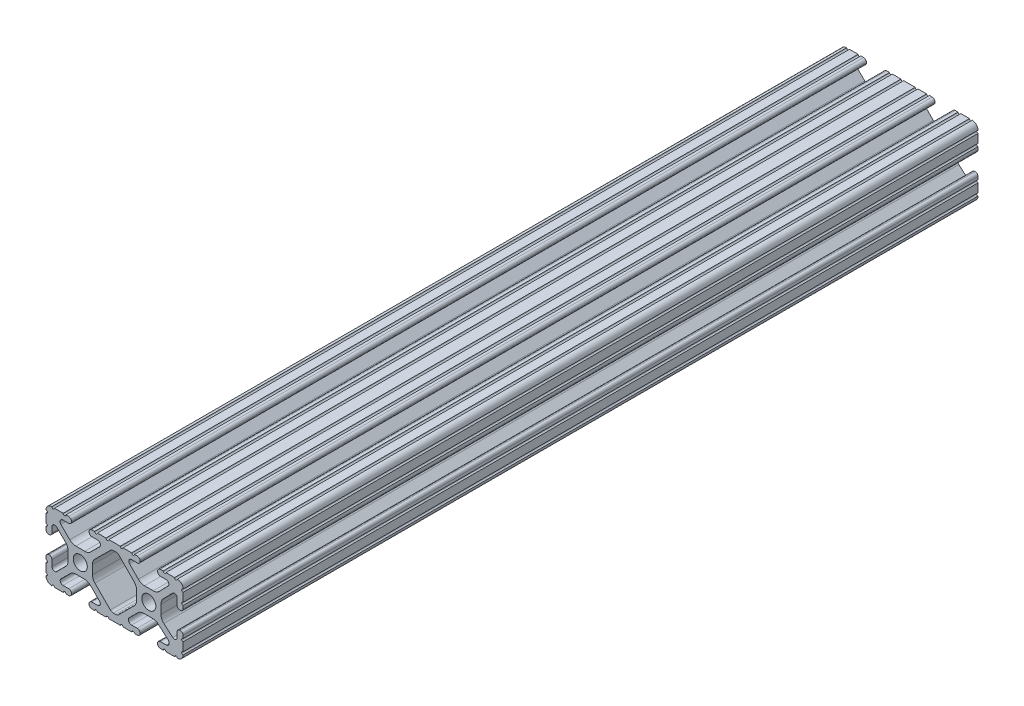
SolidWorks part; units mm, degrees
material "6061 Alloy"
ref_plane "Front Plane" through (0, 0, 0) normal (0, 0, 1) x (1, 0, 0)
ref_plane "Top Plane" through (0, 0, 0) normal (0, 1, 0) x (1, 0, 0)
ref_plane "Right Plane" through (0, 0, 0) normal (1, 0, 0) x (0, 0, -1)
sketch "Sketch1" plane through (0, 0, 0) normal (0, 0, 1) x (1, 0, 0)
  line L0 (-32.9707, 0) -> (32.2708, 0) construction
  line L1 (0, 12.7) -> (0, 0) construction
  line L2 (-12.7, 14.992) -> (-12.7, -12.6999) construction
  line L3 (12.7, 13.9801) -> (12.7, -13.3809) construction
  line L4 (-7.2595, -3.8694) -> (-1.5457, -9.5728)
  line L5 (1.5457, -9.5728) -> (7.2595, -3.8694)
  line L7 (-0.3952, 10.033) -> (0.5515, 10.033)
  line L9 (0.4332, -10.033) -> (-0.4332, -10.033)
  line L12 (8.1915, -1.6223) -> (8.1915, 1.6223)
  line L13 (7.2829, 3.8459) -> (1.6756, 9.5611)
  line L14 (-1.504, 9.5765) -> (-7.252, 3.8768)
  line L15 (-8.1915, 1.6223) -> (-8.1915, -1.6223)
  line L16 (22.2504, 12.7) -> (19.0331, 12.7)
  line L17 (18.0171, 12.7) -> (16.9875, 12.7)
  line L18 (15.9385, 11.651) -> (15.9385, 11.5392)
  line L19 (16.9875, 10.4902) -> (19.1164, 10.4902)
  line L20 (19.8441, 8.7652) -> (16.619, 5.4551)
  line L21 (14.3449, 4.4958) -> (11.0833, 4.4958)
  line L22 (8.817, 5.4472) -> (5.5642, 8.7627)
  line L23 (6.2894, 10.4902) -> (8.4125, 10.4902)
  line L24 (9.4615, 11.5392) -> (9.4615, 11.651)
  line L25 (8.4125, 12.7) -> (7.3829, 12.7)
  line L26 (6.3669, 12.7) -> (3.1496, 12.7)
  line L27 (2.1336, 12.7) -> (-2.1336, 12.7)
  line L28 (-3.1496, 12.7) -> (-6.3669, 12.7)
  line L29 (-7.3829, 12.7) -> (-8.4125, 12.7)
  line L30 (-9.4615, 11.651) -> (-9.4615, 11.5392)
  line L31 (-8.4125, 10.4902) -> (-6.2836, 10.4902)
  line L32 (-5.5326, 8.6661) -> (-8.81, 5.4163)
  line L33 (-11.0455, 4.4958) -> (-14.3545, 4.4958)
  line L34 (-16.59, 5.4163) -> (-19.8674, 8.6661)
  line L35 (-19.1164, 10.4902) -> (-16.9875, 10.4902)
  line L36 (-15.9385, 11.5392) -> (-15.9385, 11.651)
  line L37 (-16.9875, 12.7) -> (-18.0171, 12.7)
  line L38 (-19.0331, 12.7) -> (-22.2504, 12.7)
  line L39 (-25.4, 9.5504) -> (-25.4, 6.3331)
  line L40 (-25.4, 5.3171) -> (-25.4, 4.2375)
  line L41 (-24.401, 3.2385) -> (-24.2392, 3.2385)
  line L42 (-23.1902, 4.2875) -> (-23.1902, 6.3347)
  line L43 (-21.434, 7.0665) -> (-18.148, 3.8082)
  line L44 (-17.2085, 1.5536) -> (-17.2085, -1.6952)
  line L45 (-18.1405, -3.9423) -> (-21.4316, -7.2274)
  line L46 (-23.1902, -6.498) -> (-23.1902, -4.2875)
  line L47 (-24.2392, -3.2385) -> (-24.351, -3.2385)
  line L48 (-25.4, -4.2875) -> (-25.4, -5.3171)
  line L49 (-25.4, -6.3331) -> (-25.4, -9.5504)
  line L50 (-22.2504, -12.7) -> (-19.0331, -12.7)
  line L51 (-18.0171, -12.7) -> (-16.9875, -12.7)
  line L52 (-15.9384, -11.651) -> (-15.9384, -11.5392)
  line L53 (-16.9875, -10.4902) -> (-19.1164, -10.4902)
  line L54 (-19.8341, -8.7551) -> (-16.4966, -5.4237)
  line L55 (-14.2536, -4.4958) -> (-11.1464, -4.4958)
  line L56 (-8.9034, -5.4237) -> (-5.5659, -8.7551)
  line L57 (-6.2836, -10.4902) -> (-8.4125, -10.4902)
  line L58 (-9.4616, -11.5392) -> (-9.4616, -11.651)
  line L59 (-8.4125, -12.7) -> (-7.3829, -12.7)
  line L60 (-6.3669, -12.7) -> (-3.1496, -12.7)
  line L61 (-2.1336, -12.7) -> (2.1336, -12.7)
  line L62 (3.1496, -12.7) -> (6.3669, -12.7)
  line L63 (7.3829, -12.7) -> (8.4125, -12.7)
  line L64 (9.4616, -11.651) -> (9.4616, -11.5392)
  line L65 (8.4125, -10.4902) -> (6.2894, -10.4902)
  line L66 (5.4807, -8.5353) -> (8.5979, -5.4237)
  line L67 (10.8409, -4.4958) -> (14.1026, -4.4958)
  line L68 (16.1879, -5.2766) -> (19.8682, -8.4822)
  line L69 (19.1164, -10.4902) -> (16.9875, -10.4902)
  line L70 (15.9384, -11.5392) -> (15.9384, -11.651)
  line L71 (16.9875, -12.7) -> (18.0171, -12.7)
  line L72 (19.0331, -12.7) -> (22.2504, -12.7)
  line L73 (25.4, -9.5504) -> (25.4, -6.3331)
  line L74 (25.4, -5.3171) -> (25.4, -4.2375)
  line L75 (24.401, -3.2385) -> (24.1892, -3.2385)
  line L76 (23.1902, -4.2375) -> (23.1902, -6.1559)
  line L77 (21.584, -6.8869) -> (18.2982, -4.025)
  line L78 (17.2085, -1.6308) -> (17.2085, 1.6308)
  line L79 (18.1094, 3.8465) -> (21.5263, 7.3534)
  line L80 (23.1902, 6.6769) -> (23.1902, 4.2375)
  line L81 (24.1892, 3.2385) -> (24.401, 3.2385)
  line L82 (25.4, 4.2375) -> (25.4, 5.3171)
  line L83 (25.4, 6.3332) -> (25.4, 9.5504)
  circle A0 centre (-12.7, 0) radius 2.6035
  circle A1 centre (12.7, 0) radius 2.6035
  arc A2 (-0.3952, 10.033) -> (-1.504, 9.5765) centre (-0.3952, 8.4582) ccw
  arc A3 (0.5515, 10.033) -> (1.6756, 9.5611) centre (0.5515, 8.4582) cw
  arc A4 (-8.1915, -1.6223) -> (-7.2595, -3.8694) centre (-5.0165, -1.6223) ccw
  arc A5 (-0.4332, -10.033) -> (-1.5457, -9.5728) centre (-0.4332, -8.4582) cw
  arc A6 (7.2595, -3.8694) -> (8.1915, -1.6223) centre (5.0165, -1.6223) ccw
  arc A7 (8.1915, 1.6223) -> (7.2829, 3.8459) centre (5.0165, 1.6223) ccw
  arc A8 (0.4332, -10.033) -> (1.5457, -9.5728) centre (0.4332, -8.4582) ccw
  arc A9 (-7.252, 3.8768) -> (-8.1915, 1.6223) centre (-5.0165, 1.6223) ccw
  arc A16 (25.3998, 10.5664) -> (23.2664, 12.6998) centre (23.2918, 10.5918) ccw
  arc A17 (22.2504, 12.7) -> (23.2664, 12.6998) centre (22.7584, 12.7) ccw
  arc A18 (18.0171, 12.7) -> (19.0331, 12.7) centre (18.5251, 12.7) ccw
  arc A19 (16.9875, 12.7) -> (15.9385, 11.651) centre (16.9875, 11.651) ccw
  arc A20 (15.9385, 11.5392) -> (16.9875, 10.4902) centre (16.9875, 11.5392) ccw
  arc A21 (19.8441, 8.7652) -> (19.1164, 10.4902) centre (19.1164, 9.4742) ccw
  arc A22 (14.3449, 4.4958) -> (16.619, 5.4551) centre (14.3449, 7.6708) ccw
  arc A23 (8.817, 5.4472) -> (11.0833, 4.4958) centre (11.0833, 7.6708) ccw
  arc A24 (6.2894, 10.4902) -> (5.5642, 8.7627) centre (6.2894, 9.4742) ccw
  arc A25 (8.4125, 10.4902) -> (9.4615, 11.5392) centre (8.4125, 11.5392) ccw
  arc A26 (9.4615, 11.651) -> (8.4125, 12.7) centre (8.4125, 11.651) ccw
  arc A27 (6.3669, 12.7) -> (7.3829, 12.7) centre (6.8749, 12.7) ccw
  arc A28 (2.1336, 12.7) -> (3.1496, 12.7) centre (2.6416, 12.7) ccw
  arc A29 (-3.1496, 12.7) -> (-2.1336, 12.7) centre (-2.6416, 12.7) ccw
  arc A30 (-7.3829, 12.7) -> (-6.3669, 12.7) centre (-6.8749, 12.7) ccw
  arc A31 (-8.4125, 12.7) -> (-9.4615, 11.651) centre (-8.4125, 11.651) ccw
  arc A32 (-9.4615, 11.5392) -> (-8.4125, 10.4902) centre (-8.4125, 11.5392) ccw
  arc A33 (-5.5326, 8.6661) -> (-6.2836, 10.4902) centre (-6.2836, 9.4235) ccw
  arc A34 (-11.0455, 4.4958) -> (-8.81, 5.4163) centre (-11.0455, 7.6708) ccw
  arc A35 (-16.59, 5.4163) -> (-14.3545, 4.4958) centre (-14.3545, 7.6708) ccw
  arc A36 (-19.1164, 10.4902) -> (-19.8674, 8.6661) centre (-19.1164, 9.4235) ccw
  arc A37 (-16.9875, 10.4902) -> (-15.9385, 11.5392) centre (-16.9875, 11.5392) ccw
  arc A38 (-15.9385, 11.651) -> (-16.9875, 12.7) centre (-16.9875, 11.651) ccw
  arc A39 (-19.0331, 12.7) -> (-18.0171, 12.7) centre (-18.5251, 12.7) ccw
  arc A40 (-23.2664, 12.6998) -> (-22.2504, 12.7) centre (-22.7584, 12.7) ccw
  arc A41 (-23.2664, 12.6998) -> (-25.3998, 10.5664) centre (-23.2918, 10.5918) ccw
  arc A42 (-25.4, 9.5504) -> (-25.3998, 10.5664) centre (-25.4, 10.0584) ccw
  arc A43 (-25.4, 5.3171) -> (-25.4, 6.3331) centre (-25.4, 5.8251) ccw
  arc A44 (-25.4, 4.2375) -> (-24.401, 3.2385) centre (-24.401, 4.2375) ccw
  arc A45 (-24.2392, 3.2385) -> (-23.1902, 4.2875) centre (-24.2392, 4.2875) ccw
  arc A46 (-21.434, 7.0665) -> (-23.1902, 6.3347) centre (-22.1596, 6.3347) ccw
  arc A47 (-17.2085, 1.5536) -> (-18.148, 3.8082) centre (-20.3835, 1.5536) ccw
  arc A48 (-18.1405, -3.9423) -> (-17.2085, -1.6952) centre (-20.3835, -1.6952) ccw
  arc A49 (-23.1902, -6.498) -> (-21.4316, -7.2274) centre (-22.1596, -6.498) ccw
  arc A50 (-23.1902, -4.2875) -> (-24.2392, -3.2385) centre (-24.2392, -4.2875) ccw
  arc A51 (-24.351, -3.2385) -> (-25.4, -4.2875) centre (-24.351, -4.2875) ccw
  arc A52 (-25.4, -6.3331) -> (-25.4, -5.3171) centre (-25.4, -5.8251) ccw
  arc A53 (-25.3998, -10.5664) -> (-25.4, -9.5504) centre (-25.4, -10.0584) ccw
  arc A54 (-25.3998, -10.5664) -> (-23.2664, -12.6998) centre (-23.2918, -10.5918) ccw
  arc A55 (-22.2504, -12.7) -> (-23.2664, -12.6998) centre (-22.7584, -12.7) ccw
  arc A56 (-18.0171, -12.7) -> (-19.0331, -12.7) centre (-18.5251, -12.7) ccw
  arc A57 (-16.9875, -12.7) -> (-15.9384, -11.651) centre (-16.9875, -11.651) ccw
  arc A58 (-15.9384, -11.5392) -> (-16.9875, -10.4902) centre (-16.9875, -11.5392) ccw
  arc A59 (-19.8341, -8.7551) -> (-19.1164, -10.4902) centre (-19.1164, -9.4742) ccw
  arc A60 (-14.2536, -4.4958) -> (-16.4966, -5.4237) centre (-14.2536, -7.6708) ccw
  arc A61 (-8.9034, -5.4237) -> (-11.1464, -4.4958) centre (-11.1464, -7.6708) ccw
  arc A62 (-6.2836, -10.4902) -> (-5.5659, -8.7551) centre (-6.2836, -9.4742) ccw
  arc A63 (-8.4125, -10.4902) -> (-9.4616, -11.5392) centre (-8.4125, -11.5392) ccw
  arc A64 (-9.4616, -11.651) -> (-8.4125, -12.7) centre (-8.4125, -11.651) ccw
  arc A65 (-6.3669, -12.7) -> (-7.3829, -12.7) centre (-6.8749, -12.7) ccw
  arc A66 (-2.1336, -12.7) -> (-3.1496, -12.7) centre (-2.6416, -12.7) ccw
  arc A67 (3.1496, -12.7) -> (2.1336, -12.7) centre (2.6416, -12.7) ccw
  arc A68 (7.3829, -12.7) -> (6.3669, -12.7) centre (6.8749, -12.7) ccw
  arc A69 (8.4125, -12.7) -> (9.4616, -11.651) centre (8.4125, -11.651) ccw
  arc A70 (9.4616, -11.5392) -> (8.4125, -10.4902) centre (8.4125, -11.5392) ccw
  arc A71 (5.4807, -8.5353) -> (6.2894, -10.4902) centre (6.2894, -9.3455) ccw
  arc A72 (10.8409, -4.4958) -> (8.5979, -5.4237) centre (10.8409, -7.6708) ccw
  arc A73 (16.1879, -5.2766) -> (14.1026, -4.4958) centre (14.1026, -7.6708) ccw
  arc A74 (19.1164, -10.4902) -> (19.8682, -8.4822) centre (19.1164, -9.3455) ccw
  arc A75 (16.9875, -10.4902) -> (15.9384, -11.5392) centre (16.9875, -11.5392) ccw
  arc A76 (15.9384, -11.651) -> (16.9875, -12.7) centre (16.9875, -11.651) ccw
  arc A77 (19.0331, -12.7) -> (18.0171, -12.7) centre (18.5251, -12.7) ccw
  arc A78 (23.2664, -12.6998) -> (22.2504, -12.7) centre (22.7584, -12.7) ccw
  arc A79 (23.2664, -12.6998) -> (25.3998, -10.5664) centre (23.2918, -10.5918) ccw
  arc A80 (25.4, -9.5504) -> (25.3998, -10.5664) centre (25.4, -10.0584) ccw
  arc A81 (25.4, -5.3171) -> (25.4, -6.3331) centre (25.4, -5.8251) ccw
  arc A82 (25.4, -4.2375) -> (24.401, -3.2385) centre (24.401, -4.2375) ccw
  arc A83 (24.1892, -3.2385) -> (23.1902, -4.2375) centre (24.1892, -4.2375) ccw
  arc A84 (21.584, -6.8869) -> (23.1902, -6.1559) centre (22.2207, -6.1559) ccw
  arc A85 (17.2085, -1.6308) -> (18.2982, -4.025) centre (20.3835, -1.6308) ccw
  arc A86 (18.1094, 3.8465) -> (17.2085, 1.6308) centre (20.3835, 1.6308) ccw
  arc A87 (23.1902, 6.6769) -> (21.5263, 7.3534) centre (22.2207, 6.6769) ccw
  arc A88 (23.1902, 4.2375) -> (24.1892, 3.2385) centre (24.1892, 4.2375) ccw
  arc A89 (24.401, 3.2385) -> (25.4, 4.2375) centre (24.401, 4.2375) ccw
  arc A90 (25.4, 6.3332) -> (25.4, 5.3171) centre (25.4, 5.8251) ccw
  arc A91 (25.3998, 10.5664) -> (25.4, 9.5504) centre (25.4, 10.0584) ccw
  dimension "D1" = 5.207
  dimension "D6" = 6.477
  dimension "D7" = 14.859
  dimension "D14" = 1.5748
  dimension "D16" = 1.5748
  dimension "D15" = 3.175
  dimension "D2" = 25.4
  dimension "D3" = 50.8
  dimension "D4" = 25.4
  dimension "D5" = 8.2042
  dimension "D8" = 2.2098
  dimension "D9" = 2.2098
  dimension "D10" = 2.2098
  dimension "D11" = 2.2098
  dimension "D12" = 2.2098
  dimension "D13" = 6.477
extrude "Extrude1" add sketch "Sketch1" against normal blind 294.6
